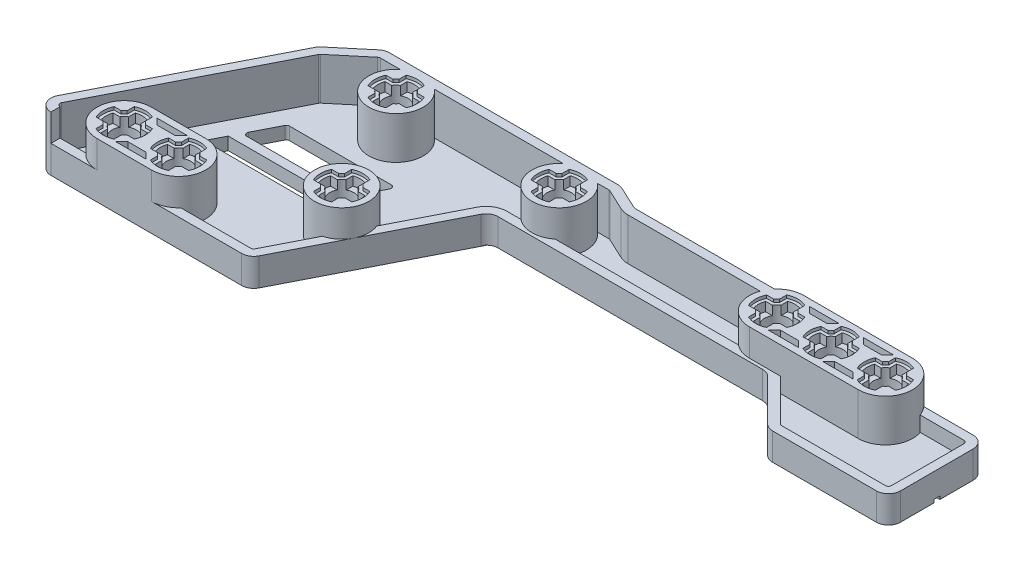
SolidWorks part; units mm, degrees
ref_plane "Front Plane" through (0, 0, 0) normal (0, 0, 1) x (1, 0, 0)
ref_plane "Top Plane" through (0, 0, 0) normal (0, 1, 0) x (1, 0, 0)
ref_plane "Right Plane" through (0, 0, 0) normal (1, 0, 0) x (0, 0, -1)
sketch "Sketch2" plane through (0, 0, 0) normal (0, 1, 0) x (1, 0, 0)
  line L0 (-9, 0) -> (9, 0) construction
  line L1 (-9, 4.5) -> (9, 4.5)
  line L2 (-9, -4.5) -> (9, -4.5)
  arc A1 (-9, 4.5) -> (-9, -4.5) centre (-9, 0) ccw
  arc A2 (9, -4.5) -> (9, 4.5) centre (9, 0) ccw
  circle A3 centre (0, 0) radius 2
  circle A4 centre (-9, 0) radius 2
  circle A5 centre (9, 0) radius 2
  point P3 (0, 0)
  point P9 (-13.5, 0)
  point P10 (13.5, 0)
  dimension "D2" = 4.5
  dimension "D3" = 4
  dimension "D1" = 27
extrude "Boss-Extrude1" add sketch "Sketch2" along normal blind 9
sketch "Sketch3" plane through (0, 9, 0) normal (0, 1, 0) x (1, 0, 0)
  line L0 (-11.8284, -1) -> (-6.1716, -1)
  line L13 (-11.8284, -1) -> (-11.8284, 1)
  line L14 (-11.8284, 1) -> (-6.1716, 1)
  line L15 (-6.1716, -1) -> (-6.1716, 1)
  line L16 (-11.8284, -1) -> (-6.1716, 1) construction
  line L17 (-11.8284, 1) -> (-6.1716, -1) construction
  line L18 (-10, -2.8284) -> (-8, -2.8284)
  line L19 (-10, -2.8284) -> (-10, 2.8284)
  line L20 (-10, 2.8284) -> (-8, 2.8284)
  line L21 (-8, -2.8284) -> (-8, 2.8284)
  line L22 (-10, -2.8284) -> (-8, 2.8284) construction
  line L23 (-10, 2.8284) -> (-8, -2.8284) construction
  circle A1 centre (-9, 0) radius 3
  circle A2 centre (-9, 0) radius 2 construction
  dimension "D4" = 6
  dimension "D3" = 2
extrude "Cut-Extrude1" cut sketch "Sketch3" against normal blind 2
sketch "Sketch4" plane through (0, 9, 0) normal (0, 1, 0) x (1, 0, 0)
  line L92 (-11, 1.5) -> (-12.1623, 1.5)
  line L93 (-12.1623, -1.5) -> (-11, -1.5)
  line L94 (-10.5, -2) -> (-10.5, -3.1623)
  line L95 (-7.5, -3.1623) -> (-7.5, -2)
  line L96 (-7, -1.5) -> (-5.8377, -1.5)
  line L97 (-5.8377, 1.5) -> (-7, 1.5)
  line L98 (-7.5, 2) -> (-7.5, 3.1623)
  line L99 (-10.5, 3.1623) -> (-10.5, 2)
  line L100 (-11, 1.5) -> (-12.1623, 1.5)
  line L101 (-12.1623, -1.5) -> (-11, -1.5)
  line L102 (-10.5, -2) -> (-10.5, -3.1623)
  line L103 (-7.5, -3.1623) -> (-7.5, -2)
  line L104 (-7, -1.5) -> (-5.8377, -1.5)
  line L105 (-5.8377, 1.5) -> (-7, 1.5)
  line L106 (-7.5, 2) -> (-7.5, 3.1623)
  line L107 (-10.5, 3.1623) -> (-10.5, 2)
  arc A100 (-12.1623, 1.5) -> (-12.1623, -1.5) centre (-9, 0) ccw
  arc A101 (-11, -1.5) -> (-10.5, -2) centre (-9, 0) ccw
  arc A102 (-10.5, -3.1623) -> (-7.5, -3.1623) centre (-9, 0) ccw
  arc A103 (-7.5, -2) -> (-7, -1.5) centre (-9, 0) ccw
  arc A104 (-5.8377, -1.5) -> (-5.8377, 1.5) centre (-9, 0) ccw
  arc A105 (-7, 1.5) -> (-7.5, 2) centre (-9, 0) ccw
  arc A106 (-7.5, 3.1623) -> (-10.5, 3.1623) centre (-9, 0) ccw
  arc A107 (-10.5, 2) -> (-11, 1.5) centre (-9, 0) ccw
  arc A108 (-12.1623, 1.5) -> (-12.1623, -1.5) centre (-9, 0) ccw
  arc A109 (-11, -1.5) -> (-10.5, -2) centre (-9, 0) ccw
  arc A110 (-10.5, -3.1623) -> (-7.5, -3.1623) centre (-9, 0) ccw
  arc A111 (-7.5, -2) -> (-7, -1.5) centre (-9, 0) ccw
  arc A112 (-5.8377, -1.5) -> (-5.8377, 1.5) centre (-9, 0) ccw
  arc A113 (-7, 1.5) -> (-7.5, 2) centre (-9, 0) ccw
  arc A114 (-7.5, 3.1623) -> (-10.5, 3.1623) centre (-9, 0) ccw
  arc A115 (-10.5, 2) -> (-11, 1.5) centre (-9, 0) ccw
  dimension "D1" = 0.5
extrude "Cut-Extrude3" cut sketch "Sketch4" against normal blind 0.5
pattern_linear "LPattern1" count 3 spacing 9 along (1, 0, 0) of "Cut-Extrude1", "Cut-Extrude3"
sketch "Sketch5" plane through (0, 9, 0) normal (0, 1, 0) x (1, 0, 0)
  line L0 (-7.003, 3.4) -> (-2.003, 3.4)
  line L1 (-2.003, 3.4) -> (-3.003, 2.4)
  line L2 (-3.003, 2.4) -> (-6.003, 2.4)
  line L3 (-6.003, 2.4) -> (-7.003, 3.4)
  line L4 (9, 4.5) -> (-9, 4.5) construction
  line L5 (-55, 0) -> (55, 0) construction
  line L6 (-3.003, -2.4) -> (-6.003, -2.4)
  line L7 (-2.003, -3.4) -> (-3.003, -2.4)
  line L8 (-7.003, -3.4) -> (-2.003, -3.4)
  line L9 (-6.003, -2.4) -> (-7.003, -3.4)
  line L10 (0, -55) -> (0, 55) construction
  line L11 (2.003, -3.4) -> (3.003, -2.4)
  line L12 (7.003, -3.4) -> (2.003, -3.4)
  line L13 (6.003, -2.4) -> (7.003, -3.4)
  line L14 (3.003, -2.4) -> (6.003, -2.4)
  line L15 (3.003, 2.4) -> (6.003, 2.4)
  line L16 (2.003, 3.4) -> (3.003, 2.4)
  line L17 (7.003, 3.4) -> (2.003, 3.4)
  line L18 (6.003, 2.4) -> (7.003, 3.4)
  dimension "D1" = 5
  dimension "D2" = 3
  dimension "D3" = 1
  dimension "D4" = 1.1
  dimension "D5" = 3.003
extrude "Cut-Extrude4" cut sketch "Sketch5" against normal blind 3
ref_plane "Plane1" through (0, 4.5, 0) normal (0, 1, 0) x (1, 0, 0)
sketch "Sketch6" plane through (0, 4.5, 0) normal (0, 1, 0) x (1, 0, 0)
  circle A54 centre (-45, 0) radius 4.5
  arc A56 (-10.7321, 1) -> (-10.7321, -1) centre (-9, 0) ccw construction
  circle A57 centre (-45, 0) radius 2
  dimension "D1" = 9
  dimension "D2" = 36
  dimension "D3" = 4
extrude "Boss-Extrude2" add sketch "Sketch6" along normal mid plane 9 separate body
sketch "Sketch8" plane through (0, 9, 0) normal (0, 1, 0) x (1, 0, 0)
  line L1 (-47.8284, 1) -> (-42.1716, 1)
  line L2 (-47.8284, 1) -> (-47.8284, -1)
  line L3 (-47.8284, -1) -> (-42.1716, -1)
  line L4 (-42.1716, 1) -> (-42.1716, -1)
  line L5 (-47.8284, 1) -> (-42.1716, -1) construction
  line L6 (-47.8284, -1) -> (-42.1716, 1) construction
  line L7 (-46, -2.8284) -> (-44, -2.8284)
  line L8 (-46, -2.8284) -> (-46, 2.8284)
  line L9 (-46, 2.8284) -> (-44, 2.8284)
  line L10 (-44, -2.8284) -> (-44, 2.8284)
  line L11 (-46, -2.8284) -> (-44, 2.8284) construction
  line L12 (-46, 2.8284) -> (-44, -2.8284) construction
  circle A0 centre (-45, 0) radius 3
  circle M11 centre (-45, 0) radius 2
  dimension "D1" = 6
  dimension "D2" = 2
extrude "Cut-Extrude5" cut sketch "Sketch8" against normal blind 2 contours L10 L9 L8 M11 | L7 L10 L8 M11 | L4 L1 L3 M11 | L2 L3 L1 M11 | L2 A0 | L9 A0 | L4 A0 | L7 A0
sketch "Sketch9" plane through (0, 9, 0) normal (0, 1, 0) x (1, 0, 0)
  line L52 (-43, -1.5) -> (-41.8377, -1.5)
  line L53 (-43.5, -3.1623) -> (-43.5, -2)
  line L54 (-46.5, -2) -> (-46.5, -3.1623)
  line L55 (-48.1623, -1.5) -> (-47, -1.5)
  line L56 (-47, 1.5) -> (-48.1623, 1.5)
  line L57 (-46.5, 3.1623) -> (-46.5, 2)
  line L58 (-43.5, 2) -> (-43.5, 3.1623)
  line L59 (-41.8377, 1.5) -> (-43, 1.5)
  line L60 (-43, -1.5) -> (-41.8377, -1.5)
  line L61 (-43.5, -3.1623) -> (-43.5, -2)
  line L62 (-46.5, -2) -> (-46.5, -3.1623)
  line L63 (-48.1623, -1.5) -> (-47, -1.5)
  line L64 (-47, 1.5) -> (-48.1623, 1.5)
  line L65 (-46.5, 3.1623) -> (-46.5, 2)
  line L66 (-43.5, 2) -> (-43.5, 3.1623)
  line L67 (-41.8377, 1.5) -> (-43, 1.5)
  arc A48 (-43.5, -2) -> (-43, -1.5) centre (-45, 0) ccw
  arc A49 (-46.5, -3.1623) -> (-43.5, -3.1623) centre (-45, 0) ccw
  arc A50 (-47, -1.5) -> (-46.5, -2) centre (-45, 0) ccw
  arc A51 (-48.1623, 1.5) -> (-48.1623, -1.5) centre (-45, 0) ccw
  arc A52 (-46.5, 2) -> (-47, 1.5) centre (-45, 0) ccw
  arc A53 (-43.5, 3.1623) -> (-46.5, 3.1623) centre (-45, 0) ccw
  arc A54 (-43, 1.5) -> (-43.5, 2) centre (-45, 0) ccw
  arc A55 (-41.8377, -1.5) -> (-41.8377, 1.5) centre (-45, 0) ccw
  arc A56 (-43.5, -2) -> (-43, -1.5) centre (-45, 0) ccw
  arc A57 (-46.5, -3.1623) -> (-43.5, -3.1623) centre (-45, 0) ccw
  arc A58 (-47, -1.5) -> (-46.5, -2) centre (-45, 0) ccw
  arc A59 (-48.1623, 1.5) -> (-48.1623, -1.5) centre (-45, 0) ccw
  arc A60 (-46.5, 2) -> (-47, 1.5) centre (-45, 0) ccw
  arc A61 (-43.5, 3.1623) -> (-46.5, 3.1623) centre (-45, 0) ccw
  arc A62 (-43, 1.5) -> (-43.5, 2) centre (-45, 0) ccw
  arc A63 (-41.8377, -1.5) -> (-41.8377, 1.5) centre (-45, 0) ccw
  dimension "D1" = 0.5
extrude "Cut-Extrude6" cut sketch "Sketch9" against normal blind 0.5
sketch "Sketch10" plane through (0, 4.5, 0) normal (0, 1, 0) x (1, 0, 0)
  circle A0 centre (-72, 0) radius 4.5
  circle A1 centre (-72, 0) radius 2
  arc A2 (-46.7321, 1) -> (-46.7321, -1) centre (-45, 0) ccw construction
  dimension "D1" = 9
  dimension "D2" = 4
  dimension "D3" = 27
extrude "Boss-Extrude3" add sketch "Sketch10" along normal mid plane 9 separate body
sketch "Sketch11" plane through (0, 9, 0) normal (0, 1, 0) x (1, 0, 0)
  line L1 (-74.8284, -1) -> (-69.1716, -1)
  line L2 (-74.8284, -1) -> (-74.8284, 1)
  line L3 (-74.8284, 1) -> (-69.1716, 1)
  line L4 (-69.1716, -1) -> (-69.1716, 1)
  line L5 (-74.8284, -1) -> (-69.1716, 1) construction
  line L6 (-74.8284, 1) -> (-69.1716, -1) construction
  line L7 (-73, -2.8284) -> (-71, -2.8284)
  line L8 (-73, -2.8284) -> (-73, 2.8284)
  line L9 (-73, 2.8284) -> (-71, 2.8284)
  line L10 (-71, -2.8284) -> (-71, 2.8284)
  line L11 (-73, -2.8284) -> (-71, 2.8284) construction
  line L12 (-73, 2.8284) -> (-71, -2.8284) construction
  circle A0 centre (-72, 0) radius 3
  circle M10 centre (-72, 0) radius 2
  dimension "D1" = 6
  dimension "D2" = 2
extrude "Cut-Extrude7" cut sketch "Sketch11" against normal blind 2 contours L10 L9 L8 M10 | L9 A0 | L1 L4 L3 M10 | L4 A0 | L7 L10 L8 M10 | L7 A0 | L3 L2 L1 M10 | L2 A0
sketch "Sketch12" plane through (0, 9, 0) normal (0, 1, 0) x (1, 0, 0)
  line L16 (-75.1623, -1.5) -> (-74, -1.5)
  line L17 (-74, 1.5) -> (-75.1623, 1.5)
  line L18 (-73.5, 3.1623) -> (-73.5, 2)
  line L19 (-70.5, 2) -> (-70.5, 3.1623)
  line L20 (-73.5, -2) -> (-73.5, -3.1623)
  line L21 (-70.5, -3.1623) -> (-70.5, -2)
  line L22 (-70, -1.5) -> (-68.8377, -1.5)
  line L23 (-68.8377, 1.5) -> (-70, 1.5)
  line L24 (-75.1623, -1.5) -> (-74, -1.5)
  line L25 (-74, 1.5) -> (-75.1623, 1.5)
  line L26 (-73.5, 3.1623) -> (-73.5, 2)
  line L27 (-70.5, 2) -> (-70.5, 3.1623)
  line L28 (-73.5, -2) -> (-73.5, -3.1623)
  line L29 (-70.5, -3.1623) -> (-70.5, -2)
  line L30 (-70, -1.5) -> (-68.8377, -1.5)
  line L31 (-68.8377, 1.5) -> (-70, 1.5)
  arc A16 (-75.1623, 1.5) -> (-75.1623, -1.5) centre (-72, 0) ccw
  arc A17 (-73.5, 2) -> (-74, 1.5) centre (-72, 0) ccw
  arc A18 (-70.5, 3.1623) -> (-73.5, 3.1623) centre (-72, 0) ccw
  arc A19 (-70, 1.5) -> (-70.5, 2) centre (-72, 0) ccw
  arc A20 (-70.5, -2) -> (-70, -1.5) centre (-72, 0) ccw
  arc A21 (-74, -1.5) -> (-73.5, -2) centre (-72, 0) ccw
  arc A22 (-73.5, -3.1623) -> (-70.5, -3.1623) centre (-72, 0) ccw
  arc A23 (-68.8377, -1.5) -> (-68.8377, 1.5) centre (-72, 0) ccw
  arc A24 (-75.1623, 1.5) -> (-75.1623, -1.5) centre (-72, 0) ccw
  arc A25 (-73.5, 2) -> (-74, 1.5) centre (-72, 0) ccw
  arc A26 (-70.5, 3.1623) -> (-73.5, 3.1623) centre (-72, 0) ccw
  arc A27 (-70, 1.5) -> (-70.5, 2) centre (-72, 0) ccw
  arc A28 (-70.5, -2) -> (-70, -1.5) centre (-72, 0) ccw
  arc A29 (-74, -1.5) -> (-73.5, -2) centre (-72, 0) ccw
  arc A30 (-73.5, -3.1623) -> (-70.5, -3.1623) centre (-72, 0) ccw
  arc A31 (-68.8377, -1.5) -> (-68.8377, 1.5) centre (-72, 0) ccw
  dimension "D1" = 0.5
extrude "Cut-Extrude8" cut sketch "Sketch12" against normal blind 0.5
sketch "Sketch13" plane through (0, 4.5, 0) normal (0, 1, 0) x (1, 0, 0)
  circle A0 centre (-63, -18) radius 4.5
  circle A1 centre (-63, -18) radius 2
  arc A2 (-70.2679, -1) -> (-70.2679, 1) centre (-72, 0) ccw construction
  circle A4 centre (-72, 0) radius 4.5 construction
  point P6 (-70, 0)
  dimension "D1" = 9
  dimension "D2" = 4
  dimension "D3" = 18
  dimension "D4" = 9
extrude "Boss-Extrude4" add sketch "Sketch13" along normal mid plane 9 separate body
sketch "Sketch14" plane through (0, 9, 0) normal (0, 1, 0) x (1, 0, 0)
  line L1 (-64, -20.8284) -> (-62, -20.8284)
  line L2 (-64, -20.8284) -> (-64, -15.1716)
  line L3 (-64, -15.1716) -> (-62, -15.1716)
  line L4 (-62, -20.8284) -> (-62, -15.1716)
  line L5 (-64, -20.8284) -> (-62, -15.1716) construction
  line L6 (-64, -15.1716) -> (-62, -20.8284) construction
  line L7 (-65.8284, -19) -> (-60.1716, -19)
  line L8 (-65.8284, -19) -> (-65.8284, -17)
  line L9 (-65.8284, -17) -> (-60.1716, -17)
  line L10 (-60.1716, -19) -> (-60.1716, -17)
  line L11 (-65.8284, -19) -> (-60.1716, -17) construction
  line L12 (-65.8284, -17) -> (-60.1716, -19) construction
  circle A0 centre (-63, -18) radius 3
  circle M11 centre (-63, -18) radius 2
  dimension "D1" = 6
  dimension "D2" = 2
extrude "Cut-Extrude9" cut sketch "Sketch14" against normal blind 2 contours L4 L3 L2 M11 | L3 A0 | L7 L10 L9 M11 | L10 A0 | L1 L4 L2 M11 | L1 A0 | L9 L8 L7 M11 | L8 A0
sketch "Sketch15" plane through (0, 9, 0) normal (0, 1, 0) x (1, 0, 0)
  line L16 (-59.8377, -16.5) -> (-61, -16.5)
  line L17 (-61, -19.5) -> (-59.8377, -19.5)
  line L18 (-61.5, -21.1623) -> (-61.5, -20)
  line L19 (-64.5, -20) -> (-64.5, -21.1623)
  line L20 (-66.1623, -19.5) -> (-65, -19.5)
  line L21 (-65, -16.5) -> (-66.1623, -16.5)
  line L22 (-64.5, -14.8377) -> (-64.5, -16)
  line L23 (-61.5, -16) -> (-61.5, -14.8377)
  line L24 (-59.8377, -16.5) -> (-61, -16.5)
  line L25 (-61, -19.5) -> (-59.8377, -19.5)
  line L26 (-61.5, -21.1623) -> (-61.5, -20)
  line L27 (-64.5, -20) -> (-64.5, -21.1623)
  line L28 (-66.1623, -19.5) -> (-65, -19.5)
  line L29 (-65, -16.5) -> (-66.1623, -16.5)
  line L30 (-64.5, -14.8377) -> (-64.5, -16)
  line L31 (-61.5, -16) -> (-61.5, -14.8377)
  arc A16 (-61, -16.5) -> (-61.5, -16) centre (-63, -18) ccw
  arc A17 (-59.8377, -19.5) -> (-59.8377, -16.5) centre (-63, -18) ccw
  arc A18 (-61.5, -20) -> (-61, -19.5) centre (-63, -18) ccw
  arc A19 (-64.5, -21.1623) -> (-61.5, -21.1623) centre (-63, -18) ccw
  arc A20 (-65, -19.5) -> (-64.5, -20) centre (-63, -18) ccw
  arc A21 (-66.1623, -16.5) -> (-66.1623, -19.5) centre (-63, -18) ccw
  arc A22 (-64.5, -16) -> (-65, -16.5) centre (-63, -18) ccw
  arc A23 (-61.5, -14.8377) -> (-64.5, -14.8377) centre (-63, -18) ccw
  arc A24 (-61, -16.5) -> (-61.5, -16) centre (-63, -18) ccw
  arc A25 (-59.8377, -19.5) -> (-59.8377, -16.5) centre (-63, -18) ccw
  arc A26 (-61.5, -20) -> (-61, -19.5) centre (-63, -18) ccw
  arc A27 (-64.5, -21.1623) -> (-61.5, -21.1623) centre (-63, -18) ccw
  arc A28 (-65, -19.5) -> (-64.5, -20) centre (-63, -18) ccw
  arc A29 (-66.1623, -16.5) -> (-66.1623, -19.5) centre (-63, -18) ccw
  arc A30 (-64.5, -16) -> (-65, -16.5) centre (-63, -18) ccw
  arc A31 (-61.5, -14.8377) -> (-64.5, -14.8377) centre (-63, -18) ccw
  dimension "D1" = 0.5
extrude "Cut-Extrude10" cut sketch "Sketch15" against normal blind 0.5
sketch "Sketch16" plane through (0, 4.5, 0) normal (0, 1, 0) x (1, 0, 0)
  line L0 (-90, -27) -> (-81, -27) construction
  line L1 (-90, -22.5) -> (-81, -22.5)
  line L2 (-90, -31.5) -> (-81, -31.5)
  arc A0 (-90, -22.5) -> (-90, -31.5) centre (-90, -27) ccw
  arc A1 (-81, -31.5) -> (-81, -22.5) centre (-81, -27) ccw
  circle A2 centre (-90, -27) radius 2
  circle A3 centre (-81, -27) radius 2
  circle A4 centre (-63, -18) radius 4.5 construction
  point P2 (-85.5, -27)
  point P7 (-94.5, -27)
  point P8 (-76.5, -27)
  dimension "D1" = 4.5
  dimension "D3" = 4
  dimension "D2" = 18
  dimension "D4" = 27
  dimension "D5" = 9
extrude "Boss-Extrude5" add sketch "Sketch16" along normal mid plane 9 separate body
sketch "Sketch17" plane through (0, 9, 0) normal (0, 1, 0) x (1, 0, 0)
  line L0 (-85.5, -22.5) -> (-85.5, -31.5) construction
  line L1 (-81, -22.5) -> (-90, -22.5) construction
  line L2 (-90, -31.5) -> (-81, -31.5) construction
  line L3 (-78.1716, -26) -> (-83.8284, -26)
  line L4 (-91, -29.8284) -> (-89, -29.8284)
  line L5 (-91, -29.8284) -> (-91, -24.1716)
  line L6 (-91, -24.1716) -> (-89, -24.1716)
  line L7 (-89, -29.8284) -> (-89, -24.1716)
  line L8 (-91, -29.8284) -> (-89, -24.1716) construction
  line L9 (-91, -24.1716) -> (-89, -29.8284) construction
  line L10 (-92.8284, -28) -> (-87.1716, -28)
  line L11 (-92.8284, -28) -> (-92.8284, -26)
  line L12 (-92.8284, -26) -> (-87.1716, -26)
  line L13 (-87.1716, -28) -> (-87.1716, -26)
  line L14 (-92.8284, -28) -> (-87.1716, -26) construction
  line L15 (-92.8284, -26) -> (-87.1716, -28) construction
  line L16 (-83.8284, -28) -> (-83.8284, -26)
  line L17 (-78.1716, -28) -> (-83.8284, -28)
  line L18 (-78.1716, -28) -> (-78.1716, -26)
  line L19 (-80, -24.1716) -> (-82, -24.1716)
  line L20 (-82, -29.8284) -> (-82, -24.1716)
  line L21 (-80, -29.8284) -> (-82, -29.8284)
  line L22 (-80, -29.8284) -> (-80, -24.1716)
  circle A0 centre (-90, -27) radius 3
  circle A1 centre (-81, -27) radius 3
  circle M11 centre (-90, -27) radius 2
  circle M16 centre (-81, -27) radius 2
  dimension "D1" = 6
  dimension "D2" = 2
extrude "Cut-Extrude11" cut sketch "Sketch17" against normal blind 2 contours L21 L22 L20 M16 | A1 L21 | L17 L3 L16 M16 | A1 L16 | L17 L18 L3 M16 | A1 L18 | L22 L19 L20 M16 | A1 L19 | L10 L13 L12 M11 | L13 A0 | L4 L7 L5 M11 | L4 A0 | L12 L11 L10 M11 | L11 A0 | L7 L6 L5 M11 | L6 A0
sketch "Sketch18" plane through (0, 9, 0) normal (0, 1, 0) x (1, 0, 0)
  line L8 (-85.5, -22.5) -> (-85.5, -31.5) construction
  line L9 (-81, -22.5) -> (-90, -22.5) construction
  line L10 (-90, -31.5) -> (-81, -31.5) construction
  line L11 (-84.1623, -25.5) -> (-83, -25.5)
  line L12 (-83, -28.5) -> (-84.1623, -28.5)
  line L13 (-82.5, -30.1623) -> (-82.5, -29)
  line L14 (-79.5, -29) -> (-79.5, -30.1623)
  line L15 (-77.8377, -28.5) -> (-79, -28.5)
  line L16 (-88.5, -25) -> (-88.5, -23.8377)
  line L17 (-86.8377, -25.5) -> (-88, -25.5)
  line L18 (-88, -28.5) -> (-86.8377, -28.5)
  line L19 (-88.5, -30.1623) -> (-88.5, -29)
  line L20 (-91.5, -29) -> (-91.5, -30.1623)
  line L21 (-93.1623, -28.5) -> (-92, -28.5)
  line L22 (-92, -25.5) -> (-93.1623, -25.5)
  line L23 (-91.5, -23.8377) -> (-91.5, -25)
  line L24 (-88.5, -25) -> (-88.5, -23.8377)
  line L25 (-86.8377, -25.5) -> (-88, -25.5)
  line L26 (-88, -28.5) -> (-86.8377, -28.5)
  line L27 (-88.5, -30.1623) -> (-88.5, -29)
  line L28 (-91.5, -29) -> (-91.5, -30.1623)
  line L29 (-93.1623, -28.5) -> (-92, -28.5)
  line L30 (-92, -25.5) -> (-93.1623, -25.5)
  line L31 (-91.5, -23.8377) -> (-91.5, -25)
  line L32 (-79, -25.5) -> (-77.8377, -25.5)
  line L33 (-79.5, -23.8377) -> (-79.5, -25)
  line L34 (-82.5, -25) -> (-82.5, -23.8377)
  arc A8 (-83, -25.5) -> (-82.5, -25) centre (-81, -27) cw
  arc A9 (-84.1623, -28.5) -> (-84.1623, -25.5) centre (-81, -27) cw
  arc A10 (-82.5, -29) -> (-83, -28.5) centre (-81, -27) cw
  arc A11 (-79.5, -30.1623) -> (-82.5, -30.1623) centre (-81, -27) cw
  arc A12 (-79, -28.5) -> (-79.5, -29) centre (-81, -27) cw
  arc A13 (-77.8377, -25.5) -> (-77.8377, -28.5) centre (-81, -27) cw
  arc A14 (-79.5, -25) -> (-79, -25.5) centre (-81, -27) cw
  arc A15 (-82.5, -23.8377) -> (-79.5, -23.8377) centre (-81, -27) cw
  arc A16 (-88, -25.5) -> (-88.5, -25) centre (-90, -27) ccw
  arc A17 (-86.8377, -28.5) -> (-86.8377, -25.5) centre (-90, -27) ccw
  arc A18 (-88.5, -29) -> (-88, -28.5) centre (-90, -27) ccw
  arc A19 (-91.5, -30.1623) -> (-88.5, -30.1623) centre (-90, -27) ccw
  arc A20 (-92, -28.5) -> (-91.5, -29) centre (-90, -27) ccw
  arc A21 (-93.1623, -25.5) -> (-93.1623, -28.5) centre (-90, -27) ccw
  arc A22 (-91.5, -25) -> (-92, -25.5) centre (-90, -27) ccw
  arc A23 (-88.5, -23.8377) -> (-91.5, -23.8377) centre (-90, -27) ccw
  arc A24 (-88, -25.5) -> (-88.5, -25) centre (-90, -27) ccw
  arc A25 (-86.8377, -28.5) -> (-86.8377, -25.5) centre (-90, -27) ccw
  arc A26 (-88.5, -29) -> (-88, -28.5) centre (-90, -27) ccw
  arc A27 (-91.5, -30.1623) -> (-88.5, -30.1623) centre (-90, -27) ccw
  arc A28 (-92, -28.5) -> (-91.5, -29) centre (-90, -27) ccw
  arc A29 (-93.1623, -25.5) -> (-93.1623, -28.5) centre (-90, -27) ccw
  arc A30 (-91.5, -25) -> (-92, -25.5) centre (-90, -27) ccw
  arc A31 (-88.5, -23.8377) -> (-91.5, -23.8377) centre (-90, -27) ccw
  dimension "D1" = 0.5
extrude "Cut-Extrude12" cut sketch "Sketch18" against normal blind 0.5
sketch "Sketch19" plane through (0, 0, 0) normal (0, 1, 0) x (1, 0, 0)
  line L0 (9, 4.5) -> (-9, 4.5) construction
  line L1 (9, 4.5) -> (-9, 4.5)
  line L2 (12.3541, 3) -> (22.5, 3)
  line L3 (22.5, 3) -> (22.5, -13)
  line L4 (22.5, -13) -> (2.5, -13)
  line L5 (2.5, -13) -> (-5.5, -5)
  line L6 (-12.3541, 3) -> (-35.5523, 3)
  line L7 (-35.5523, 3) -> (-39.8413, 5)
  line L8 (-39.8413, 5) -> (-78.8413, 5)
  line L9 (-78.8413, 5) -> (-84.8634, -0.0531)
  line L10 (-84.8634, -0.0531) -> (-100.8864, -31.5)
  line L11 (-100.8864, -31.5) -> (-64.8281, -31.5)
  line L12 (-64.8281, -31.5) -> (-51.3257, -5)
  line L13 (-51.3257, -5) -> (-5.5, -5)
  line L15 (-9, -4.5) -> (9, -4.5) construction
  line L16 (-90, -31.5) -> (-81, -31.5) construction
  arc A0 (-9, 4.5) -> (-9, -4.5) centre (-9, 0) ccw construction
  arc A1 (9, -4.5) -> (9, 4.5) centre (9, 0) ccw construction
  arc A2 (-9, 4.5) -> (-12.3541, 3) centre (-9, 0) ccw
  arc A3 (12.3541, 3) -> (9, 4.5) centre (9, 0) ccw
  circle A4 centre (-63, -18) radius 4.5 construction
  circle A5 centre (-90, -27) radius 2
  circle A6 centre (-81, -27) radius 2
  circle A7 centre (-63, -18) radius 2
  circle A8 centre (-72, 0) radius 2
  circle A9 centre (-45, 0) radius 2
  circle A10 centre (-9, 0) radius 2
  circle A11 centre (0, 0) radius 2
  circle A12 centre (9, 0) radius 2
  circle A13 centre (-72, 0) radius 4.5 construction
  point P13 (13.5, 0)
  dimension "D14" = 4
  dimension "D1" = 8
  dimension "D2" = 9
  dimension "D3" = 16
  dimension "D4" = 20
  dimension "D5" = 45
  dimension "D6" = 0.5
  dimension "D7" = 25
  dimension "D8" = 39
  dimension "D9" = 23.1982
  dimension "D10" = 40
  dimension "D11" = 63
  dimension "D12" = 63
  dimension "D13" = 35.2937
  dimension "D15" = 5
extrude "Boss-Extrude6" add sketch "Sketch19" along normal blind 2
fillet "Fillet1" radius 2 11 edges at (-100.8864, 1, 31.5) (-64.8281, 1, 31.5) (22.5, 1, -3) (22.5, 1, 13) (2.5, 1, 13) (-5.5, 1, 5) (-51.3257, 1, 5) (-35.5523, 1, -3) (-39.8413, 1, -5) (-78.8413, 1, -5) (-84.8634, 1, 0.0531)
sketch "Sketch20" plane through (0, 2, 0) normal (0, 1, 0) x (1, 0, 0)
  line L4 (-97.6227, -31.5) -> (-90, -31.5) construction
  line L6 (-81, -31.5) -> (-66.0537, -31.5) construction
  line L7 (-64.2717, -30.408) -> (-58.9905, -20.043) construction
  line L8 (-58.9905, -20.043) -> (-51.8821, -6.092) construction
  line L9 (-50.1001, -5) -> (-6.3284, -5) construction
  line L10 (-4.9142, -5.5858) -> (1.9142, -12.4142) construction
  line L11 (3.3284, -13) -> (20.5, -13) construction
  line L12 (22.5, -11) -> (22.5, 1) construction
  line L13 (20.5, 3) -> (12.3541, 3) construction
  line L32 (-90, -31.5) -> (-81, -31.5) construction
  line L33 (-4.9142, -5.5858) -> (1.9142, -12.4142)
  line L34 (3.3284, -13) -> (20.5, -13)
  line L35 (22.5, -11) -> (22.5, 1)
  line L36 (20.5, 3) -> (12.3541, 3)
  line L37 (-50.1001, -5) -> (-6.3284, -5)
  line L38 (-58.9905, -20.043) -> (-51.8821, -6.092)
  line L39 (-64.2717, -30.408) -> (-58.9905, -20.043)
  line L40 (-81, -31.5) -> (-66.0537, -31.5)
  line L41 (-90, -31.5) -> (-81, -31.5)
  line L42 (-97.6227, -31.5) -> (-90, -31.5)
  arc A6 (-66.0537, -31.5) -> (-64.2717, -30.408) centre (-66.0537, -29.5) ccw construction
  arc A8 (-50.1001, -5) -> (-51.8821, -6.092) centre (-50.1001, -7) ccw construction
  arc A9 (-4.9142, -5.5858) -> (-6.3284, -5) centre (-6.3284, -7) ccw construction
  arc A10 (1.9142, -12.4142) -> (3.3284, -13) centre (3.3284, -11) ccw construction
  arc A11 (20.5, -13) -> (22.5, -11) centre (20.5, -11) ccw construction
  arc A12 (22.5, 1) -> (20.5, 3) centre (20.5, 1) ccw construction
  arc A32 (-4.9142, -5.5858) -> (-6.3284, -5) centre (-6.3284, -7) ccw
  arc A33 (1.9142, -12.4142) -> (3.3284, -13) centre (3.3284, -11) ccw
  arc A34 (20.5, -13) -> (22.5, -11) centre (20.5, -11) ccw
  arc A35 (22.5, 1) -> (20.5, 3) centre (20.5, 1) ccw
  arc A36 (-50.1001, -5) -> (-51.8821, -6.092) centre (-50.1001, -7) ccw
  arc A37 (-66.0537, -31.5) -> (-64.2717, -30.408) centre (-66.0537, -29.5) ccw
extrude "Extrude-Thin1" add sketch "Sketch20" along normal blind 2.5 thin thin type one direction reverse wall 1.5
sketch "Sketch21" plane through (0, 2, 0) normal (0, 1, 0) x (1, 0, 0)
  line L0 (-12.3541, 3) -> (-35.1089, 3) construction
  line L1 (-35.9542, 3.1874) -> (-39.4395, 4.8126) construction
  line L2 (-40.2847, 5) -> (-78.1134, 5) construction
  line L3 (-79.399, 4.5321) -> (-84.5517, 0.2084) construction
  line L4 (-85.0481, -0.4157) -> (-99.4047, -28.592) construction
  line L5 (-12.3541, 3) -> (-35.1089, 3)
  line L6 (-35.9542, 3.1874) -> (-39.4395, 4.8126)
  line L7 (-40.2847, 5) -> (-78.1134, 5)
  line L8 (-79.399, 4.5321) -> (-84.5517, 0.2084)
  line L9 (-85.0481, -0.4157) -> (-99.4047, -28.592)
  arc A0 (-35.9542, 3.1874) -> (-35.1089, 3) centre (-35.1089, 5) ccw construction
  arc A1 (-39.4395, 4.8126) -> (-40.2847, 5) centre (-40.2847, 3) ccw construction
  arc A2 (-78.1134, 5) -> (-79.399, 4.5321) centre (-78.1134, 3) ccw construction
  arc A3 (-84.5517, 0.2084) -> (-85.0481, -0.4157) centre (-83.2661, -1.3237) ccw construction
  arc A4 (-99.4047, -28.592) -> (-97.6227, -31.5) centre (-97.6227, -29.5) ccw construction
  arc A5 (-35.9542, 3.1874) -> (-35.1089, 3) centre (-35.1089, 5) ccw
  arc A6 (-39.4395, 4.8126) -> (-40.2847, 5) centre (-40.2847, 3) ccw
  arc A7 (-78.1134, 5) -> (-79.399, 4.5321) centre (-78.1134, 3) ccw
  arc A8 (-84.5517, 0.2084) -> (-85.0481, -0.4157) centre (-83.2661, -1.3237) ccw
  arc A9 (-99.4047, -28.592) -> (-97.6227, -31.5) centre (-97.6227, -29.5) ccw
extrude "Extrude-Thin2" add sketch "Sketch21" along normal blind 7 thin thin type one direction reverse wall 1.5
sketch "Sketch22" plane through (0, 9, 0) normal (0, 1, 0) x (1, 0, 0)
  line L0 (-88, -23.6) -> (-87, -24.6)
  line L1 (-87, -24.6) -> (-84, -24.6)
  line L2 (-84, -24.6) -> (-83, -23.6)
  line L3 (-83, -23.6) -> (-88, -23.6)
  line L4 (-81, -22.5) -> (-90, -22.5) construction
  line L5 (-90, -27) -> (-81, -27) construction
  line L6 (-83, -30.4) -> (-88, -30.4)
  line L7 (-84, -29.4) -> (-83, -30.4)
  line L12 (-87, -29.4) -> (-84, -29.4)
  line L13 (-88, -30.4) -> (-87, -29.4)
  arc A1 (-88.2679, -28) -> (-88.2679, -26) centre (-90, -27) ccw construction
  dimension "D1" = 5
  dimension "D2" = 3
  dimension "D3" = 1
  dimension "D4" = 1.1
  dimension "D5" = 3
  dimension "D6" = 135
extrude "Cut-Extrude13" cut sketch "Sketch22" against normal blind 3
sketch "Sketch23" plane through (0, 2, 0) normal (0, 1, 0) x (1, 0, 0)
  line L0 (-86.5, -13.284) -> (-87.862, -15.957)
  line L1 (-87.862, -15.957) -> (-69.862, -15.957)
  line L2 (-69.862, -15.957) -> (-68.5, -13.284)
  line L3 (-68.5, -13.284) -> (-86.5, -13.284)
  line L5 (-87.862, -15.957) -> (-81.5591, -3.587) construction
  line L6 (-84.9198, -11.784) -> (-68.0421, -11.784)
  line L8 (-82.8817, -6.784) -> (-66.004, -6.784)
  line L10 (-85.3653, -11.057) -> (-83.3272, -7.057)
  line L11 (-69.862, -15.957) -> (-63.9629, -4.3795) construction
  line L12 (-67.5966, -11.511) -> (-65.5585, -7.511)
  arc A0 (-86.8377, -28.5) -> (-86.8377, -25.5) centre (-90, -27) ccw construction
  arc A1 (-58.8042, -16.3734) -> (-61.8497, -22.3505) centre (-63, -18) ccw construction
  arc A4 (-83.3272, -7.057) -> (-82.8817, -6.784) centre (-82.8817, -7.284) cw
  arc A5 (-84.9198, -11.784) -> (-85.3653, -11.057) centre (-84.9198, -11.284) cw
  arc A6 (-65.5585, -7.511) -> (-66.004, -6.784) centre (-66.004, -7.284) ccw
  arc A7 (-67.5966, -11.511) -> (-68.0421, -11.784) centre (-68.0421, -11.284) cw
  point P10 (-86.5, -27)
  point P14 (-67.0095, -15.957)
  point P17 (-65.1881, -6.784)
  point P23 (-83.1881, -6.784)
  point P27 (-85.7357, -11.784)
  point P30 (-67.7357, -11.784)
  dimension "D5" = 0.5
  dimension "D6" = 0.5
  dimension "D1" = 63
  dimension "D2" = 3
  dimension "D3" = 18
  dimension "D4" = 1.5
  dimension "D7" = 5
extrude "Cut-Extrude14" cut sketch "Sketch23" against normal up to surface (2 mm away) up to face at (-31.819, 0, 5.7082)
sketch "Sketch25" plane through (0, 0, 0) normal (0, -1, 0) x (1, 0, 0)
  circle A5 centre (-81, 27) radius 2.5
  circle A6 centre (-81, 27) radius 2.5
  circle A8 centre (-90, 27) radius 2.5
  circle A9 centre (-90, 27) radius 2.5
  circle A11 centre (-63, 18) radius 2.5
  circle A12 centre (-63, 18) radius 2.5
  circle A14 centre (-72, 0) radius 2.5
  circle A15 centre (-72, 0) radius 2.5
  circle A30 centre (-45, 0) radius 2.5
  circle A31 centre (-45, 0) radius 2.5
  circle A33 centre (-9, 0) radius 2.5
  circle A34 centre (-9, 0) radius 2.5
  circle A36 centre (0, 0) radius 2.5
  circle A37 centre (0, 0) radius 2.5
  circle A39 centre (9, 0) radius 2.5
  circle A40 centre (9, 0) radius 2.5
  dimension "D1" = 0.5
  dimension "D2" = 0.5
  dimension "D3" = 0.5
  dimension "D4" = 0.5
  dimension "D5" = 0.5
  dimension "D6" = 0.5
  dimension "D7" = 0.5
  dimension "D8" = 0.5
extrude "Cut-Extrude15" cut sketch "Sketch25" against normal blind 0.5
sketch "Sketch27" plane through (0, 0, 0) normal (0, -1, 0) x (1, 0, 0)
  line L0 (22.5, 4.5006) -> (-2.5945, 4.5006)
  line L2 (-2.5945, 4.5006) -> (-4.0951, 3)
  line L3 (-4.0951, 3) -> (-49.1017, 3)
  line L4 (22.5, 4.5006) -> (22.5, 5.4994)
  line L6 (22.5, 11) -> (22.5, -1) construction
  line L7 (22.5, 5.4994) -> (-3.01, 5.4994)
  line L8 (-3.01, 5.4994) -> (-4.5094, 4)
  line L9 (-4.5094, 4) -> (-49.1017, 4)
  line L10 (-49.1017, 4) -> (-49.1017, 3)
  line L11 (-50.1001, 5) -> (-6.3284, 5) construction
  point P14 (22.5, 5)
  point P15 (22.5, 5)
  dimension "D1" = 1
  dimension "D2" = 45
  dimension "D3" = 0.9987
  dimension "D4" = 1
  dimension "D5" = 25.51
  dimension "D6" = 25.0945
  dimension "D7" = 1
  dimension "D8" = 0.9984
extrude "Cut-Extrude18" cut sketch "Sketch27" against normal blind 0.5
fillet "Fillet2" radius 0.5 4 edges at (-2.5945, 0.25, 4.5006) (-4.0951, 0.25, 3) (-4.5094, 0.25, 4) (-3.01, 0.25, 5.4994)
sketch "Sketch28" plane through (0, 0, 0) normal (0, -1, 0) x (1, 0, 0)
  line L0 (-40.2847, -5) -> (-78.1134, -5) construction
  line L1 (-79.399, -4.5321) -> (-84.5517, -0.2084) construction
  line L2 (-85.0481, 0.4157) -> (-99.4047, 28.592) construction
  line L3 (-97.6227, 31.5) -> (-66.0537, 31.5) construction
  line L4 (-64.2717, 30.408) -> (-51.8821, 6.092) construction
  line L5 (-50.7781, -5) -> (-78.1134, -5)
  line L6 (-79.399, -4.5321) -> (-84.5517, -0.2084)
  line L7 (-85.0481, 0.4157) -> (-99.4047, 28.592)
  line L8 (-97.6227, 31.5) -> (-66.0537, 31.5)
  line L9 (-64.2717, 30.408) -> (-51.8821, 6.092)
  line L10 (-85.3653, 11.057) -> (-83.3272, 7.057) construction
  line L11 (-82.8817, 6.784) -> (-66.004, 6.784) construction
  line L12 (-65.5585, 7.511) -> (-67.5966, 11.511) construction
  line L13 (-68.0421, 11.784) -> (-84.9198, 11.784) construction
  line L14 (-87.862, 15.957) -> (-86.5, 13.284) construction
  line L15 (-86.5, 13.284) -> (-68.5, 13.284) construction
  line L16 (-68.5, 13.284) -> (-69.862, 15.957) construction
  line L17 (-69.862, 15.957) -> (-87.862, 15.957) construction
  line L18 (-85.3653, 11.057) -> (-83.3272, 7.057)
  line L19 (-82.8817, 6.784) -> (-66.004, 6.784)
  line L20 (-65.5585, 7.511) -> (-67.5966, 11.511)
  line L21 (-68.0421, 11.784) -> (-84.9198, 11.784)
  line L22 (-87.862, 15.957) -> (-86.5, 13.284)
  line L23 (-86.5, 13.284) -> (-68.5, 13.284)
  line L24 (-68.5, 13.284) -> (-69.862, 15.957)
  line L25 (-69.862, 15.957) -> (-87.862, 15.957)
  line L26 (-51.8821, 6.092) -> (-48.9961, 0.4278)
  line L27 (-48.7781, -0.4802) -> (-48.7781, -3)
  arc A0 (-79.399, -4.5321) -> (-78.1134, -5) centre (-78.1134, -3) ccw construction
  arc A1 (-85.0481, 0.4157) -> (-84.5517, -0.2084) centre (-83.2661, 1.3237) ccw construction
  arc A2 (-97.6227, 31.5) -> (-99.4047, 28.592) centre (-97.6227, 29.5) ccw construction
  arc A3 (-64.2717, 30.408) -> (-66.0537, 31.5) centre (-66.0537, 29.5) ccw construction
  arc A4 (-79.399, -4.5321) -> (-78.1134, -5) centre (-78.1134, -3) ccw
  arc A5 (-85.0481, 0.4157) -> (-84.5517, -0.2084) centre (-83.2661, 1.3237) ccw
  arc A6 (-97.6227, 31.5) -> (-99.4047, 28.592) centre (-97.6227, 29.5) ccw
  arc A7 (-64.2717, 30.408) -> (-66.0537, 31.5) centre (-66.0537, 29.5) ccw
  circle A8 centre (-90, 27) radius 2.5 construction
  circle A9 centre (-81, 27) radius 2.5 construction
  circle A10 centre (-72, 0) radius 2.5 construction
  circle A11 centre (-63, 18) radius 2.5 construction
  circle A12 centre (-90, 27) radius 2.5
  circle A13 centre (-81, 27) radius 2.5
  circle A14 centre (-72, 0) radius 2.5
  circle A15 centre (-63, 18) radius 2.5
  arc A16 (-67.5966, 11.511) -> (-68.0421, 11.784) centre (-68.0421, 11.284) ccw construction
  arc A17 (-66.004, 6.784) -> (-65.5585, 7.511) centre (-66.004, 7.284) ccw construction
  arc A18 (-83.3272, 7.057) -> (-82.8817, 6.784) centre (-82.8817, 7.284) ccw construction
  arc A19 (-84.9198, 11.784) -> (-85.3653, 11.057) centre (-84.9198, 11.284) ccw construction
  arc A20 (-67.5966, 11.511) -> (-68.0421, 11.784) centre (-68.0421, 11.284) ccw
  arc A21 (-66.004, 6.784) -> (-65.5585, 7.511) centre (-66.004, 7.284) ccw
  arc A22 (-83.3272, 7.057) -> (-82.8817, 6.784) centre (-82.8817, 7.284) ccw
  arc A23 (-84.9198, 11.784) -> (-85.3653, 11.057) centre (-84.9198, 11.284) ccw
  arc A24 (-48.7781, -3) -> (-50.7781, -5) centre (-50.7781, -3) cw
  arc A25 (-48.9961, 0.4278) -> (-48.7781, -0.4802) centre (-50.7781, -0.4802) cw
  point P45 (-48.7781, 0)
  dimension "D2" = 2
  dimension "D3" = 2
  dimension "D1" = 63
extrude "Boss-Extrude7" add sketch "Sketch28" along normal blind 0.1
ref_plane "Plane2" through (22.5, 0, 0) normal (1, 0, 0) x (0, 0, -1)
mirror "Mirror6" [suppressed] about plane through (22.5, 0, 0) normal (1, 0, 0)
sketch "Sketch29" [suppressed] plane through (0, 0, 0) normal (0, 1, 0) x (1, 0, 0)
  line L0 (-12.3541, 3) -> (-35.1089, 3) construction
  line L1 (22.5, 15.7847) -> (-100.5836, 15.7847)
  line L2 (22.5, 15.7847) -> (22.5, -51.9005)
  line L3 (22.5, -51.9005) -> (-100.5836, -51.9005)
  line L4 (-100.5836, 15.7847) -> (-100.5836, -51.9005)
  dimension "D1" = 123.0836
  dimension "D2" = 67.6852
  dimension "D3" = 12.7847
extrude "Cut-Extrude19" [suppressed] cut sketch "Sketch29" against normal through all both and the other way through all
sketch "Sketch30" [suppressed] plane through (0, 2, 0) normal (0, 1, 0) x (1, 0, 0)
  line L0 (36, 0) -> (54, 0) construction
  line L1 (36, 4.5) -> (54, 4.5)
  line L2 (36, -4.5) -> (54, -4.5)
  line L3 (126, -27) -> (135, -27) construction
  line L4 (126, -22.5) -> (135, -22.5)
  line L5 (126, -31.5) -> (135, -31.5)
  arc A0 (36, 4.5) -> (36, -4.5) centre (36, 0) ccw
  arc A1 (54, -4.5) -> (54, 4.5) centre (54, 0) ccw
  circle A2 centre (90, 0) radius 4.5
  circle A3 centre (117, 0) radius 4.5
  circle A4 centre (108, -18) radius 4.5
  arc A5 (126, -22.5) -> (126, -31.5) centre (126, -27) ccw
  arc A6 (135, -31.5) -> (135, -22.5) centre (135, -27) ccw
  circle A7 centre (36, 0) radius 2
  circle A8 centre (45, 0) radius 2
  circle A9 centre (54, 0) radius 2
  circle A10 centre (90, 0) radius 2
  circle A11 centre (117, 0) radius 2
  circle A12 centre (108, -18) radius 2
  circle A13 centre (126, -27) radius 2
  circle A14 centre (135, -27) radius 2
  point P2 (45, 0)
  point P22 (130.5, -27)
  dimension "D1" = 4.5
  dimension "D2" = 9
  dimension "D3" = 4.5
  dimension "D4" = 4
extrude "Boss-Extrude8" [suppressed] add sketch "Sketch30" along normal blind 7
sketch "Sketch31" [suppressed] plane through (0, 9, 0) normal (0, 1, 0) x (1, 0, 0)
  line L1 (44, -2.8284) -> (46, -2.8284)
  line L2 (44, -2.8284) -> (44, 2.8284)
  line L3 (44, 2.8284) -> (46, 2.8284)
  line L4 (46, -2.8284) -> (46, 2.8284)
  line L5 (44, -2.8284) -> (46, 2.8284) construction
  line L6 (44, 2.8284) -> (46, -2.8284) construction
  line L7 (42.1716, -1) -> (47.8284, -1)
  line L8 (42.1716, -1) -> (42.1716, 1)
  line L9 (42.1716, 1) -> (47.8284, 1)
  line L10 (47.8284, -1) -> (47.8284, 1)
  line L11 (42.1716, -1) -> (47.8284, 1) construction
  line L12 (42.1716, 1) -> (47.8284, -1) construction
  circle A0 centre (45, 0) radius 3
  circle M35 centre (45, 0) radius 2
  dimension "D1" = 6
  dimension "D2" = 2
extrude "Cut-Extrude20" [suppressed] cut sketch "Sketch31" against normal blind 2 contours L4 L3 L2 M35 | L7 L10 L9 M35 | L1 L4 L2 M35 | L9 L8 L7 M35 | L8 A0 | L3 A0 | L10 A0 | L1 A0
sketch "Sketch32" [suppressed] plane through (0, 9, 0) normal (0, 1, 0) x (1, 0, 0)
  line L16 (43, 1.5) -> (41.8377, 1.5)
  line L17 (41.8377, -1.5) -> (43, -1.5)
  line L18 (43.5, -2) -> (43.5, -3.1623)
  line L19 (46.5, -3.1623) -> (46.5, -2)
  line L20 (47, -1.5) -> (48.1623, -1.5)
  line L21 (48.1623, 1.5) -> (47, 1.5)
  line L22 (46.5, 2) -> (46.5, 3.1623)
  line L23 (43.5, 3.1623) -> (43.5, 2)
  line L24 (43, 1.5) -> (41.8377, 1.5)
  line L25 (41.8377, -1.5) -> (43, -1.5)
  line L26 (43.5, -2) -> (43.5, -3.1623)
  line L27 (46.5, -3.1623) -> (46.5, -2)
  line L28 (47, -1.5) -> (48.1623, -1.5)
  line L29 (48.1623, 1.5) -> (47, 1.5)
  line L30 (46.5, 2) -> (46.5, 3.1623)
  line L31 (43.5, 3.1623) -> (43.5, 2)
  arc A16 (43.5, 2) -> (43, 1.5) centre (45, 0) ccw
  arc A17 (41.8377, 1.5) -> (41.8377, -1.5) centre (45, 0) ccw
  arc A18 (43, -1.5) -> (43.5, -2) centre (45, 0) ccw
  arc A19 (43.5, -3.1623) -> (46.5, -3.1623) centre (45, 0) ccw
  arc A20 (46.5, -2) -> (47, -1.5) centre (45, 0) ccw
  arc A21 (48.1623, -1.5) -> (48.1623, 1.5) centre (45, 0) ccw
  arc A22 (47, 1.5) -> (46.5, 2) centre (45, 0) ccw
  arc A23 (46.5, 3.1623) -> (43.5, 3.1623) centre (45, 0) ccw
  arc A24 (43.5, 2) -> (43, 1.5) centre (45, 0) ccw
  arc A25 (41.8377, 1.5) -> (41.8377, -1.5) centre (45, 0) ccw
  arc A26 (43, -1.5) -> (43.5, -2) centre (45, 0) ccw
  arc A27 (43.5, -3.1623) -> (46.5, -3.1623) centre (45, 0) ccw
  arc A28 (46.5, -2) -> (47, -1.5) centre (45, 0) ccw
  arc A29 (48.1623, -1.5) -> (48.1623, 1.5) centre (45, 0) ccw
  arc A30 (47, 1.5) -> (46.5, 2) centre (45, 0) ccw
  arc A31 (46.5, 3.1623) -> (43.5, 3.1623) centre (45, 0) ccw
  dimension "D1" = 0.5
extrude "Cut-Extrude21" [suppressed] cut sketch "Sketch32" against normal blind 0.5
sketch "Sketch33" [suppressed] plane through (0, 9, 0) normal (0, 1, 0) x (1, 0, 0)
  point P0 (36, 0)
  point P1 (54, 0)
  point P3 (90, 0)
  point P5 (117, 0)
  point P7 (108, -18)
  point P9 (126, -27)
  point P11 (135, -27)
pattern_sketch "Sketch-Pattern1" [suppressed]
sketch "Sketch34" [suppressed] plane through (0, 9, 0) normal (0, 1, 0) x (1, 0, 0)
  line L0 (126, -27) -> (135, -27) construction
  line L1 (128, -23.6) -> (133, -23.6)
  line L2 (133, -23.6) -> (132, -24.6)
  line L3 (132, -24.6) -> (129, -24.6)
  line L4 (129, -24.6) -> (128, -23.6)
  line L5 (135, -22.5) -> (126, -22.5) construction
  line L6 (132, -29.4) -> (129, -29.4)
  line L7 (133, -30.4) -> (132, -29.4)
  line L8 (128, -30.4) -> (133, -30.4)
  line L9 (129, -29.4) -> (128, -30.4)
  line L10 (45, 4.5) -> (45, -4.5) construction
  line L11 (54, 4.5) -> (36, 4.5) construction
  line L12 (36, -4.5) -> (54, -4.5) construction
  line L13 (31.5, 0) -> (58.5, 0) construction
  line L14 (38, 3.4) -> (43, 3.4)
  line L15 (43, 3.4) -> (42, 2.4)
  line L16 (42, 2.4) -> (39, 2.4)
  line L17 (39, 2.4) -> (38, 3.4)
  line L18 (42, -2.4) -> (39, -2.4)
  line L19 (43, -3.4) -> (42, -2.4)
  line L20 (38, -3.4) -> (43, -3.4)
  line L21 (39, -2.4) -> (38, -3.4)
  line L22 (47, -3.4) -> (48, -2.4)
  line L23 (52, -3.4) -> (47, -3.4)
  line L24 (51, -2.4) -> (52, -3.4)
  line L25 (48, -2.4) -> (51, -2.4)
  line L26 (48, 2.4) -> (51, 2.4)
  line L27 (47, 3.4) -> (48, 2.4)
  line L28 (52, 3.4) -> (47, 3.4)
  line L29 (51, 2.4) -> (52, 3.4)
  arc A0 (36, 4.5) -> (36, -4.5) centre (36, 0) ccw construction
  arc A1 (56.8284, -3.5) -> (58.2426, 1.5) centre (54, 0) ccw construction
  arc A2 (37.7321, -1) -> (37.7321, 1) centre (36, 0) ccw construction
  dimension "D1" = 5
  dimension "D2" = 3
  dimension "D3" = 1
  dimension "D4" = 1.1
  dimension "D5" = 3
  dimension "D6" = 5
  dimension "D7" = 3
  dimension "D8" = 1
  dimension "D9" = 1.1
  dimension "D10" = 3
extrude "Cut-Extrude22" [suppressed] cut sketch "Sketch34" against normal blind 3
